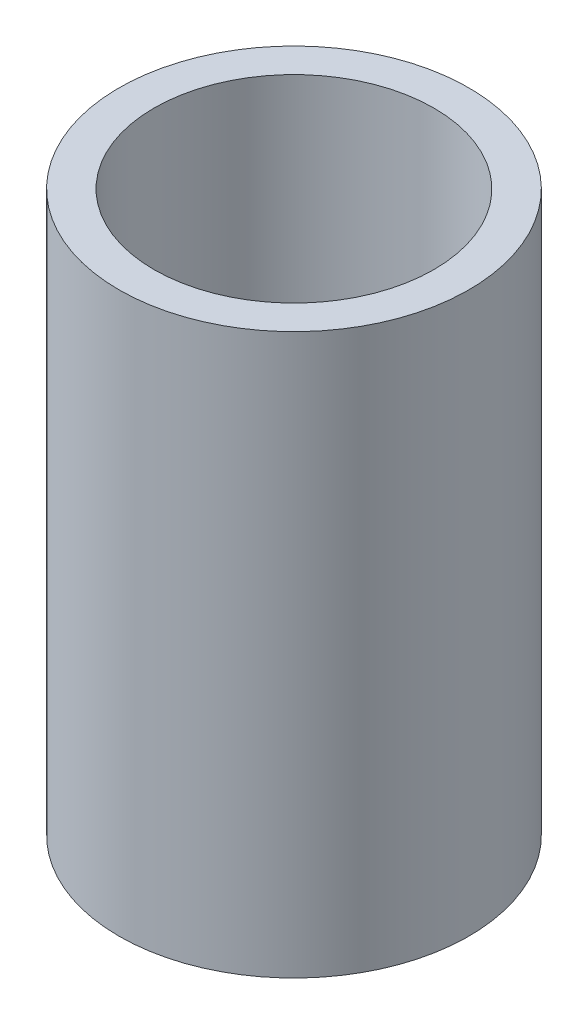
SolidWorks part; units mm, degrees
ref_plane "Front Plane" through (0, 0, 0) normal (0, 0, 1) x (1, 0, 0)
ref_plane "Top Plane" through (0, 0, 0) normal (0, 1, 0) x (1, 0, 0)
ref_plane "Right Plane" through (0, 0, 0) normal (1, 0, 0) x (0, 0, -1)
sketch "Sketch1" plane through (0, 0, 0) normal (0, 1, 0) x (1, 0, 0)
  circle A0 centre (0, 0) radius 6
  circle A1 centre (0, 0) radius 7.5
  dimension "D1" = 15
  dimension "D2" = 12
extrude "Boss-Extrude1" add sketch "Sketch1" along normal mid plane 24
